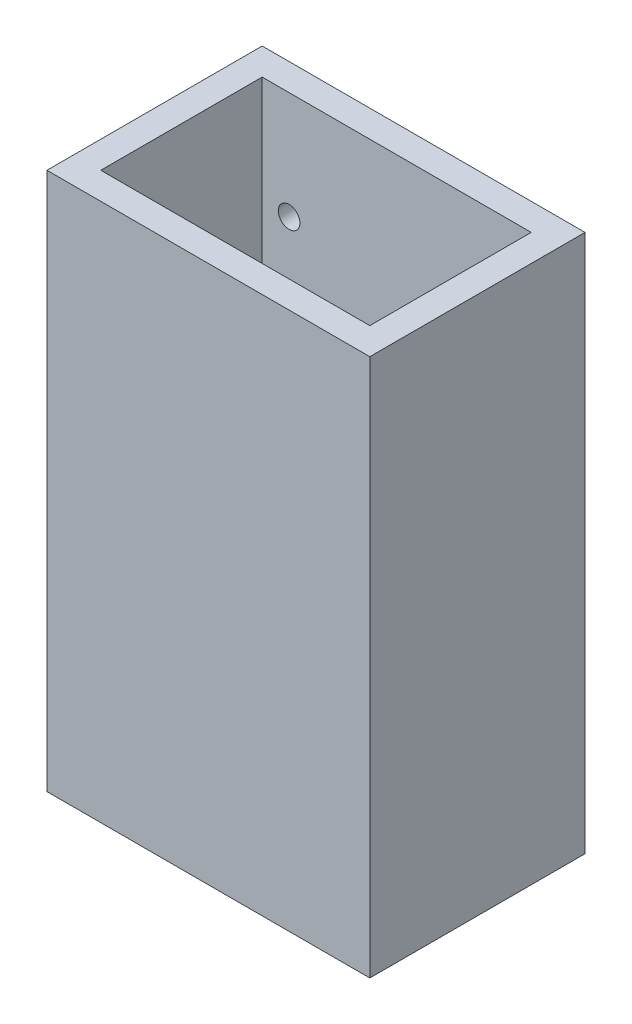
SolidWorks part; units mm, degrees
ref_plane "Front Plane" through (0, 0, 0) normal (0, 0, 1) x (1, 0, 0)
ref_plane "Top Plane" through (0, 0, 0) normal (0, 1, 0) x (1, 0, 0)
ref_plane "Right Plane" through (0, 0, 0) normal (1, 0, 0) x (0, 0, -1)
sketch "Sketch1" plane through (0, 0, 0) normal (0, 1, 0) x (1, 0, 0)
  line L0 (-31.75, 19.05) -> (31.75, 19.05)
  line L1 (-38.1, -25.4) -> (38.1, -25.4)
  line L2 (-38.1, -25.4) -> (-38.1, 25.4)
  line L3 (-38.1, 25.4) -> (38.1, 25.4)
  line L4 (38.1, -25.4) -> (38.1, 25.4)
  line L5 (-38.1, -25.4) -> (38.1, 25.4) construction
  line L6 (-38.1, 25.4) -> (38.1, -25.4) construction
  line L7 (31.75, -19.05) -> (31.75, 19.05)
  line L8 (-31.75, -19.05) -> (31.75, -19.05)
  line L9 (-31.75, -19.05) -> (-31.75, 19.05)
  point P0 (0, 0)
  dimension "D1" = 50.8
  dimension "D2" = 76.2
  dimension "D3" = 6.35
extrude "Boss-Extrude1" add sketch "Sketch1" along normal blind 127
sketch "Sketch2" plane through (0, 0, -25.4) normal (0, 0, -1) x (-1, 0, 0)
  line L0 (-25.4, 101.6) -> (-25.4, 25.4)
  line L1 (-38.1, 127) -> (38.1, 127) construction
  line L2 (-38.1, 0) -> (38.1, 0) construction
  line L3 (0, 0) -> (0, 127) construction
  line L4 (-38.1, 127) -> (-38.1, 0) construction
  line L5 (25.4, 101.6) -> (25.4, 25.4)
  dimension "D1" = 76.2
  dimension "D2" = 25.4
  dimension "D3" = 12.7
hole_wizard "1/4-20 Tapped Hole1" positions "Sketch3" profile "Sketch4" tap size "1/4-20" standard "ANSI Inch" end condition up to next
sketch "Sketch3" plane through (0, 0, -25.4) normal (0, 0, -1) x (-1, 0, 0)
  point P0 (-25.4, 101.6)
  point P3 (-25.4, 25.4)
  point P6 (25.4, 25.4)
  point P9 (25.4, 101.6)
sketch "Sketch4" plane through (25.4, 101.6, -25.4) normal (1, 0, 0) x (0, 1, 0)
  line L0 (0, 0) -> (0, 6.35)
  line L1 (0, 6.35) -> (2.5527, 6.35)
  line L2 (2.5527, 6.35) -> (2.5527, 0)
  line L5 (2.5527, 0) -> (0, 0)
  line L11 (0, -6.35) -> (0, 107.95) construction
  dimension "Thru Tap Drill Dia." = 5.1054
  dimension "Thru Tap Drill Depth" = 6.35
cosmetic thread "Hole Thread1" parameters "D2"=6.35
cosmetic thread "Hole Thread2" parameters "D2"=6.35
cosmetic thread "Hole Thread3" parameters "D2"=6.35
cosmetic thread "Hole Thread4" parameters "D2"=6.35
